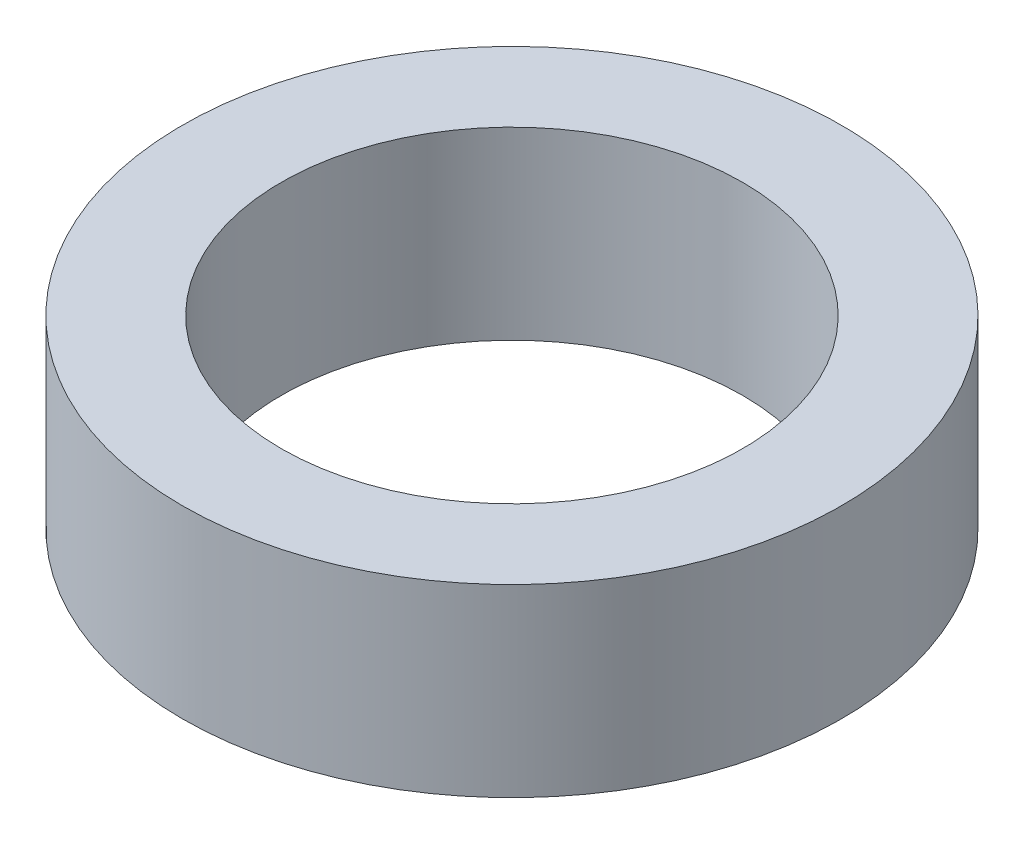
SolidWorks part; units mm, degrees
ref_plane "Front Plane" through (0, 0, 0) normal (0, 0, 1) x (1, 0, 0)
ref_plane "Top Plane" through (0, 0, 0) normal (0, 1, 0) x (1, 0, 0)
ref_plane "Right Plane" through (0, 0, 0) normal (1, 0, 0) x (0, 0, -1)
sketch "Sketch1" plane through (0, 0, 0) normal (0, 1, 0) x (1, 0, 0)
  circle A0 centre (0, 0) radius 12.7
  circle A1 centre (0, 0) radius 8.89
  dimension "D1" = 3.81
extrude "Boss-Extrude1" add sketch "Sketch1" along normal blind 7.112
